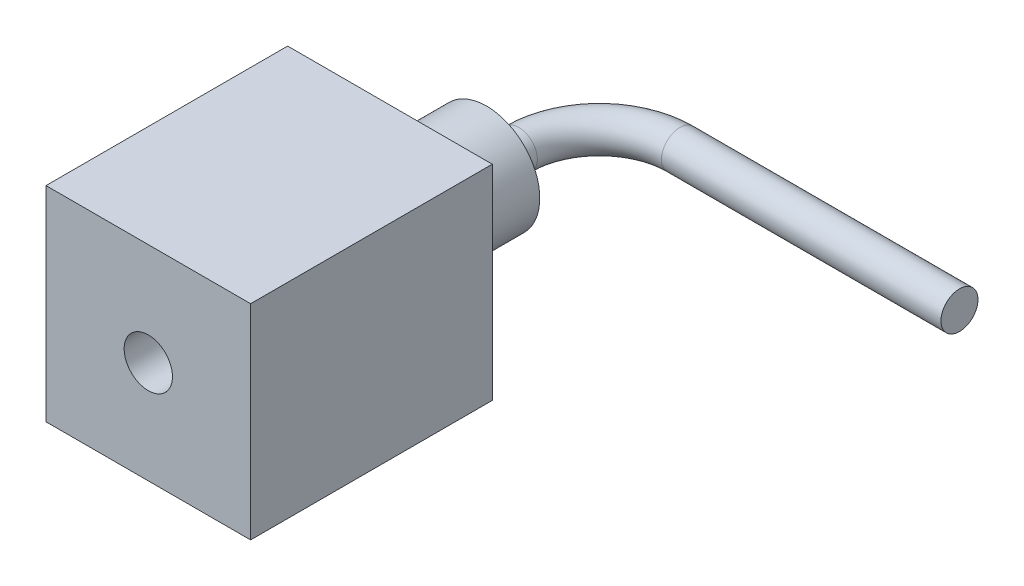
SolidWorks part; units mm, degrees
ref_plane "Front Plane" through (0, 0, 0) normal (0, 0, 1) x (1, 0, 0)
ref_plane "Top Plane" through (0, 0, 0) normal (0, 1, 0) x (1, 0, 0)
ref_plane "Right Plane" through (0, 0, 0) normal (1, 0, 0) x (0, 0, -1)
sketch "Sketch1" plane through (0, 0, 0) normal (0, 0, 1) x (1, 0, 0)
  line L1 (1.27, -1.27) -> (-1.27, -1.27)
  line L2 (1.27, -1.27) -> (1.27, 1.27)
  line L3 (1.27, 1.27) -> (-1.27, 1.27)
  line L4 (-1.27, -1.27) -> (-1.27, 1.27)
  line L5 (1.27, -1.27) -> (-1.27, 1.27) construction
  line L6 (1.27, 1.27) -> (-1.27, -1.27) construction
  point P0 (0, 0)
  dimension "D1" = 2.54
extrude "Boss-Extrude1" add sketch "Sketch1" along normal blind 3
sketch "Sketch2" plane through (0, 0, 0) normal (0, 0, -1) x (-1, 0, 0)
  circle A0 centre (0, 0) radius 0.66
  dimension "D1" = 1.32
extrude "Boss-Extrude2" add sketch "Sketch2" along normal blind 1.2
sketch "Sketch3" plane through (0, 0, -1.2) normal (0, 0, -1) x (-1, 0, 0)
  circle A0 centre (0, 0) radius 0.23
  dimension "D1" = 0.46
sketch "Sketch4" plane through (0, 0, 3) normal (0, 0, 1) x (1, 0, 0)
  circle A0 centre (0, 0) radius 0.3
  dimension "D1" = 0.6
extrude "Cut-Extrude1" cut sketch "Sketch4" against normal blind 4
sketch "Sketch5" plane through (0, 0, 0) normal (0, 1, 0) x (1, 0, 0)
  line L0 (0, -3) -> (0, 1.6)
  line L1 (1.27, -3) -> (-1.27, -3) construction
  line L2 (1, 2.6) -> (4.47, 2.6)
  line L3 (1.27, -3) -> (1.27, 0) construction
  arc A0 (1, 2.6) -> (0, 1.6) centre (1, 1.6) ccw
  dimension "D3" = 1
  dimension "D1" = 5.6
  dimension "D2" = 3.2
sweep "Sweep1" add profiles "Sketch3" path "Sketch5"
